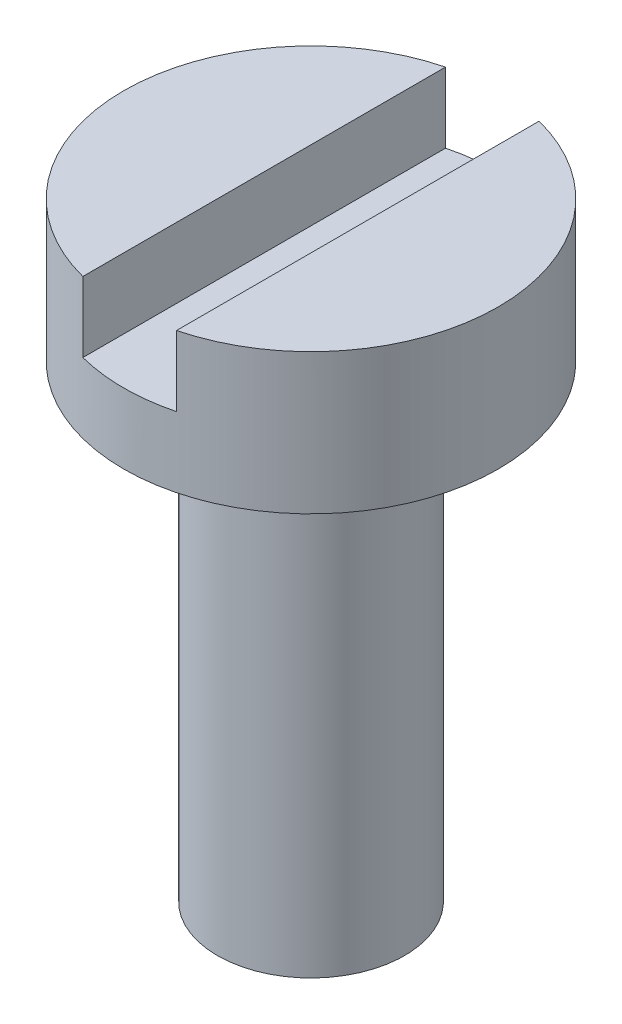
SolidWorks part; units mm, degrees
ref_plane "Front Plane" through (0, 0, 0) normal (0, 0, 1) x (1, 0, 0)
ref_plane "Top Plane" through (0, 0, 0) normal (0, 1, 0) x (1, 0, 0)
ref_plane "Right Plane" through (0, 0, 0) normal (1, 0, 0) x (0, 0, -1)
sketch "Sketch1" plane through (0, 0, 0) normal (0, 1, 0) x (1, 0, 0)
  circle A0 centre (0, 0) radius 4
extrude "Extrude1" add sketch "Sketch1" along normal blind 3
sketch "Sketch2" plane through (0, 3, 0) normal (0, 1, 0) x (-1, 0, 0)
  line L0 (0, -4) -> (0, 4) construction
  line L2 (0, 4.4012) -> (-1, 4.4012)
  line L3 (-1, 4.4012) -> (-1, -5.0783)
  line L4 (-1, -5.0783) -> (1, -5.0783)
  line L5 (1, -5.0783) -> (1, 4.4012)
  line L6 (1, 4.4012) -> (0, 4.4012)
  circle A0 centre (0, 0) radius 4 construction
extrude "Cut-Extrude1" cut sketch "Sketch2" against normal blind 1.5
sketch "Sketch3" plane through (0, 0, 0) normal (0, -1, 0) x (1, 0, 0)
  circle A0 centre (0, 0) radius 2
extrude "Extrude2" add sketch "Sketch3" along normal blind 10
